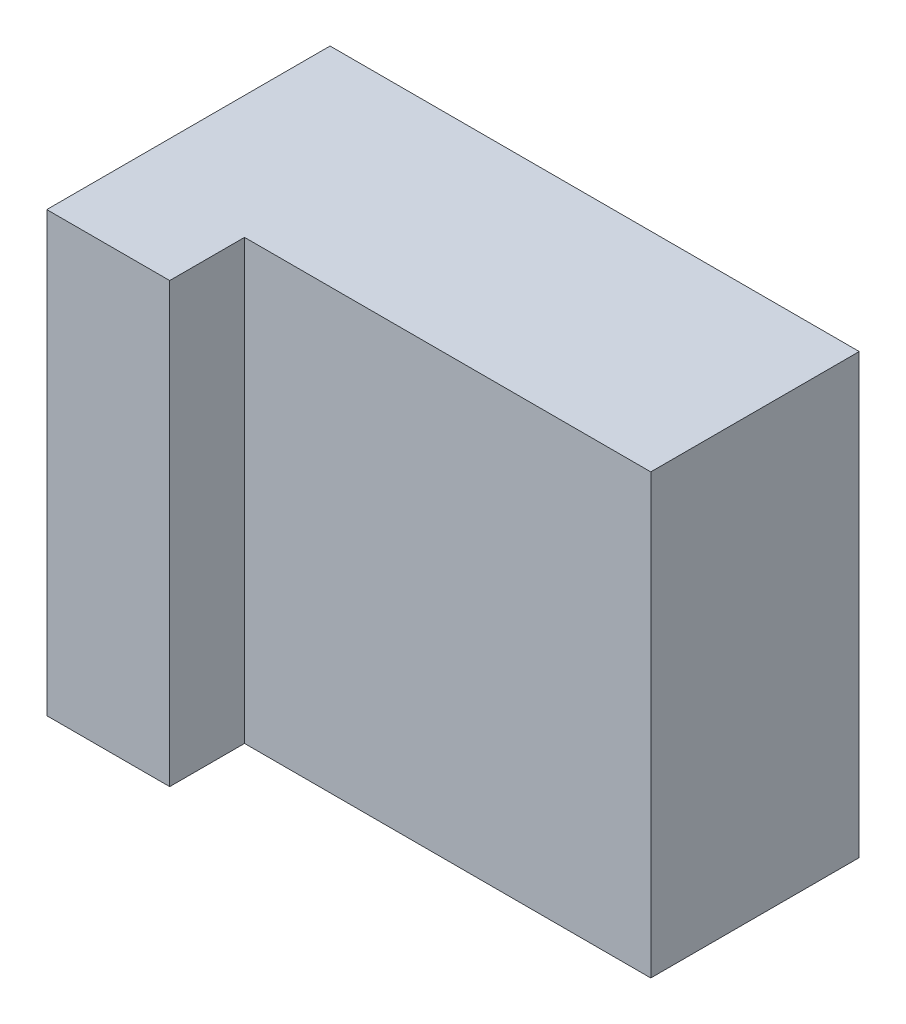
SolidWorks part; units mm, degrees
ref_plane "Plan de face" through (0, 0, 0) normal (0, 0, 1) x (1, 0, 0)
ref_plane "Plan de dessus" through (0, 0, 0) normal (0, 1, 0) x (1, 0, 0)
ref_plane "Plan de droite" through (0, 0, 0) normal (1, 0, 0) x (0, 0, -1)
sketch "Esquisse1" plane through (0, 0, 0) normal (0, 0, 1) x (1, 0, 0)
  line L0 (22, 82) -> (22, 81)
  line L1 (0, 0) -> (22, 0)
  line L2 (0, 0) -> (0, 82)
  line L3 (0, 82) -> (22, 82)
  line L4 (22, 0) -> (22, 82) construction
  line L5 (1, 81) -> (21, 81)
  line L6 (1, 81) -> (1, 1)
  line L7 (1, 1) -> (21, 1)
  line L8 (21, 81) -> (21, 1) construction
  line L9 (22, 81) -> (21, 81)
  line L10 (22, 0) -> (22, 1)
  line L11 (22, 1) -> (21, 1)
  dimension "D1" = 82
  dimension "D2" = 22
  dimension "D3" = 80
  dimension "D4" = 1
  dimension "D5" = 20
  dimension "D6" = 1
extrude "Boss.-Extru.1" add sketch "Esquisse1" along normal blind 52
sketch "Esquisse2" plane through (0, 0, 52) normal (0, 0, 1) x (1, 0, 0)
  line L1 (0, 82) -> (22, 82)
  line L2 (0, 82) -> (0, 0)
  line L3 (0, 0) -> (22, 0)
  line L4 (22, 82) -> (22, 0)
extrude "Boss.-Extru.2" add sketch "Esquisse2" along normal blind 1
sketch "Esquisse3" plane through (22, 0, 0) normal (1, 0, 0) x (0, 0, -1)
  line L0 (-53, 82) -> (0, 82) construction
  line L1 (-53, 0) -> (-35, 0)
  line L2 (-53, 0) -> (-53, 82)
  line L3 (-53, 82) -> (-35, 82)
  line L4 (-35, 0) -> (-35, 82)
  dimension "D1" = 18
extrude "Boss.-Extru.3" add sketch "Esquisse3" along normal blind 1
sketch "Esquisse5" plane through (23, 0, 0) normal (1, 0, 0) x (0, 0, -1)
  line L0 (-53, 0) -> (-35, 0) construction
  line L1 (-39, 0) -> (0, 0)
  line L2 (-39, 0) -> (-39, 82)
  line L3 (-39, 82) -> (0, 82)
  line L4 (0, 0) -> (0, 82) construction
  line L5 (0, 0) -> (0, 1)
  line L6 (-35, 1) -> (0, 1)
  line L7 (-35, 1) -> (-35, 81)
  line L8 (-35, 81) -> (0, 81)
  line L9 (0, 1) -> (0, 81) construction
  line L10 (0, 81) -> (0, 82)
  dimension "D1" = 39
extrude "Boss.-Extru.4" add sketch "Esquisse5" along normal blind 75 and the other way up to next
sketch "Esquisse6" plane through (98, 0, 0) normal (1, 0, 0) x (0, 0, -1)
  line L1 (-39, 0) -> (0, 0)
  line L2 (-39, 0) -> (-39, 82)
  line L3 (-39, 82) -> (0, 82)
  line L4 (0, 0) -> (0, 82)
extrude "Boss.-Extru.5" add sketch "Esquisse6" along normal blind 1
